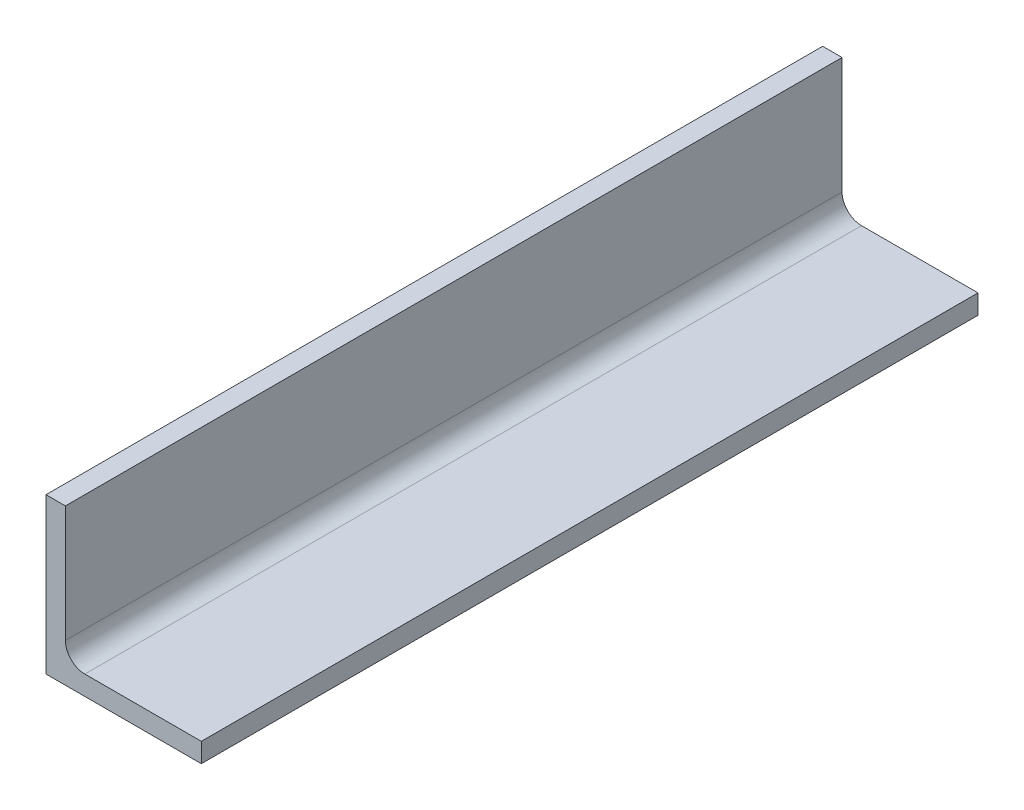
SolidWorks part; units mm, degrees
ref_plane "Front Plane" through (0, 0, 0) normal (0, 0, 1) x (1, 0, 0)
ref_plane "Top Plane" through (0, 0, 0) normal (0, 1, 0) x (1, 0, 0)
ref_plane "Right Plane" through (0, 0, 0) normal (1, 0, 0) x (0, 0, -1)
sketch "Sketch2" plane through (0, 0, 0) normal (0, 0, 1) x (1, 0, 0)
  line L0 (0, 0) -> (0, 50.8)
  line L1 (0, 50.8) -> (6.35, 50.8)
  line L2 (6.35, 50.8) -> (6.35, 12.7)
  line L3 (12.7, 6.35) -> (50.8, 6.35)
  line L4 (50.8, 6.35) -> (50.8, 0)
  line L5 (50.8, 0) -> (0, 0)
  arc A0 (12.7, 6.35) -> (6.35, 12.7) centre (12.7, 12.7) cw
  dimension "D4" = 6.35
  dimension "D1" = 6.35
  dimension "D2" = 50.8
  dimension "D3" = 50.8
extrude "Boss-Extrude1" add sketch "Sketch2" along normal mid plane 254
